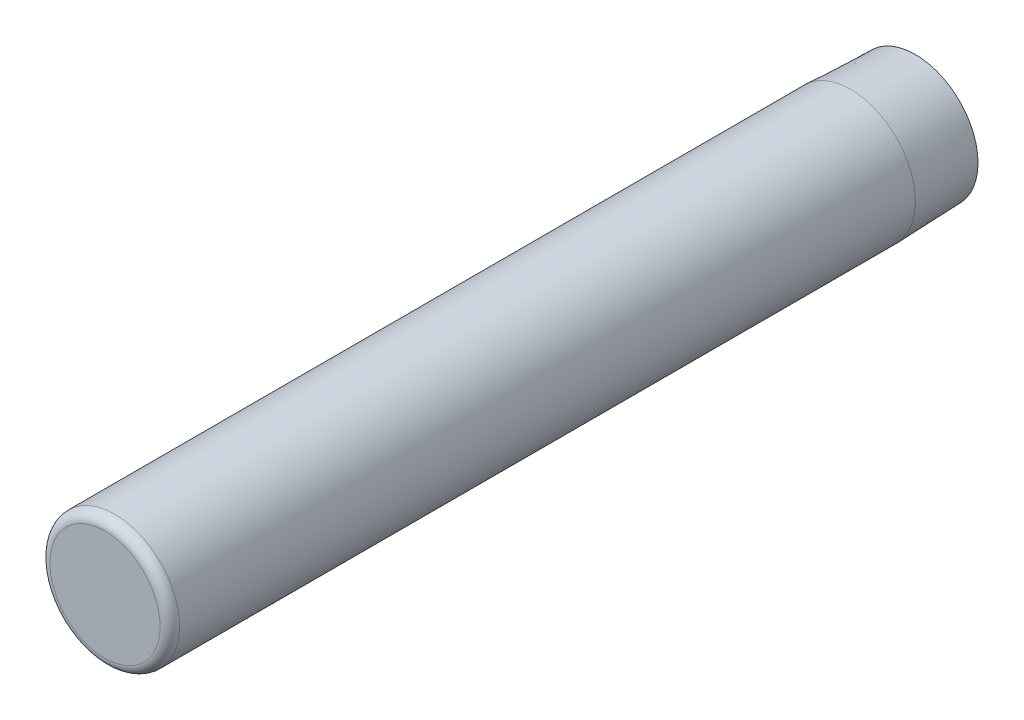
SolidWorks part; units mm, degrees
material "Acero al carbono no aleado"
ref_plane "Alzado" through (0, 0, 0) normal (0, 0, 1) x (1, 0, 0)
ref_plane "Planta" through (0, 0, 0) normal (0, 1, 0) x (1, 0, 0)
ref_plane "Vista lateral" through (0, 0, 0) normal (1, 0, 0) x (0, 0, -1)
sketch "Croquis1" plane through (0, 0, 0) normal (0, 0, 1) x (1, 0, 0)
  circle A0 centre (0, 0) radius 2
  dimension "D1" = 4
extrude "Saliente-Extruir1" add sketch "Croquis1" along normal blind 25
chamfer "Chaflán1" distance 2 angle 2 1 edges at (2, 0, 0)
fillet "Redondeo1" radius 0.3 1 edges at (2, 0, 25)
